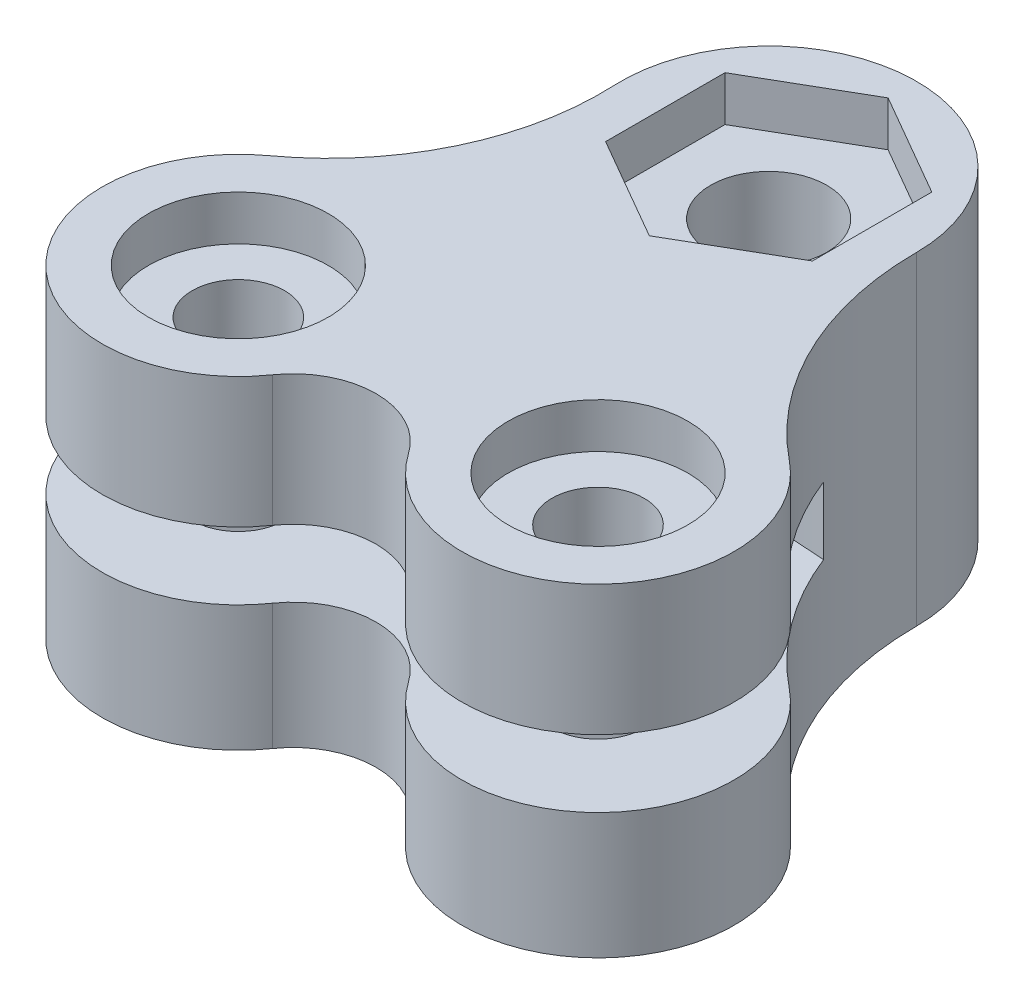
SolidWorks part; units mm, degrees
ref_plane "Front Plane" through (0, 0, 0) normal (0, 0, 1) x (1, 0, 0)
ref_plane "Top Plane" through (0, 0, 0) normal (0, 1, 0) x (1, 0, 0)
ref_plane "Right Plane" through (0, 0, 0) normal (1, 0, 0) x (0, 0, -1)
sketch "Sketch1" plane through (0, 0, 0) normal (0, 1, 0) x (1, 0, 0)
  line L0 (0, 0) -> (0, 133.35) construction
  line L1 (0, 157.5) -> (-10.448, 157.1531) construction
  line L2 (-12.7, 132.7439) -> (-12.7, 142.3578) construction
  line L3 (12.7, 132.7439) -> (12.7, 142.3578) construction
  line L4 (-12.7, 132.7439) -> (-3.0861, 132.7439) construction
  line L5 (12.7, 132.7439) -> (3.0861, 132.7439) construction
  line L6 (0, 157.5) -> (10.4521, 157.5) construction
  line L7 (-12.7, 132.7439) -> (-12.7, 123.13) construction
  line L8 (12.7, 132.7439) -> (12.7, 123.13) construction
  line L9 (-12.7, 132.7439) -> (-18.3509, 140.5217) construction
  line L10 (12.7, 132.7439) -> (18.3509, 140.5217) construction
  circle A0 centre (0, 0) radius 133.35 construction
  circle A1 centre (-12.7, 132.7439) radius 3.2639
  circle A2 centre (12.7, 132.7439) radius 3.2639
  arc A3 (-18.3509, 140.5217) -> (-4.8072, 127.2547) centre (-12.7, 132.7439) ccw
  arc A4 (18.3509, 140.5217) -> (4.8072, 127.2547) centre (12.7, 132.7439) cw
  circle A5 centre (0, 0) radius 157.5 construction
  circle A6 centre (0, 157.5) radius 4.1021
  arc A7 (10.4463, 157.1532) -> (-10.4403, 157.0036) centre (0, 157.5) ccw
  arc A8 (-10.448, 157.1531) -> (-18.3509, 140.5217) centre (-29.6618, 156.0897) cw
  arc A9 (10.4521, 157.5) -> (18.7238, 140.2366) centre (32.6027, 157.5) ccw
  arc A10 (4.8072, 127.2547) -> (-4.8072, 127.2547) centre (0, 123.9116) ccw
  dimension "D1" = 266.7
  dimension "D2" = 6.5278
  dimension "D5" = 315
  dimension "D6" = 8.2042
  dimension "D3" = 12.7
  dimension "D4" = 6.35
  dimension "D7" = 6.35
  dimension "D8" = 36
  dimension "D9" = 36
extrude "Boss-Extrude1" add sketch "Sketch1" along normal blind 22.86
ref_plane "Plane1" through (0, 8.89, 0) normal (0, -1, 0) x (-1, 0, 0)
sketch "Sketch2" plane through (0, 8.89, 0) normal (0, -1, 0) x (-1, 0, 0)
  circle A0 centre (0, 0) radius 149.225 construction
  arc A1 (-18.7238, 140.2366) -> (-4.8072, 127.2547) centre (-12.7, 132.7439) ccw construction
  arc A2 (4.8072, 127.2547) -> (-4.8072, 127.2547) centre (0, 123.9116) ccw construction
  arc A3 (4.8072, 127.2547) -> (18.3509, 140.5217) centre (12.7, 132.7439) ccw construction
  arc A4 (10.4403, 157.0036) -> (18.3509, 140.5217) centre (29.6618, 156.0897) ccw construction
  arc A5 (-18.7238, 140.2366) -> (-10.4521, 157.5) centre (-32.6027, 157.5) ccw construction
  arc A6 (-18.7238, 140.2366) -> (-4.8072, 127.2547) centre (-12.7, 132.7439) ccw
  arc A7 (4.8072, 127.2547) -> (-4.8072, 127.2547) centre (0, 123.9116) ccw
  arc A8 (4.8072, 127.2547) -> (18.3509, 140.5217) centre (12.7, 132.7439) ccw
  arc A9 (11.6154, 149.4092) -> (18.3509, 140.5217) centre (29.6618, 156.0897) ccw
  arc A10 (-18.7238, 140.2366) -> (-11.9944, 149.3792) centre (-32.6027, 157.5) ccw
  arc A11 (11.6154, 149.4092) -> (-11.9944, 149.3792) centre (0, 0) ccw
  circle A13 centre (0, 0) radius 149.86 construction
  point P18 (151.13, 0)
  dimension "D1" = 298.45
  dimension "D2" = 0.635
extrude "Cut-Extrude1" cut sketch "Sketch2" against normal blind 4.7625
sketch "Sketch3" plane through (0, 0, 0) normal (0, -1, 0) x (1, 0, 0)
  line L0 (-12.7, -132.7439) -> (-12.7, -125.9614) construction
  line L1 (-18.5737, -129.3526) -> (-18.5738, -136.1351)
  line L2 (-18.5738, -136.1351) -> (-12.7, -139.5263)
  line L3 (-12.7, -139.5263) -> (-6.8263, -136.1351)
  line L4 (-6.8263, -136.1351) -> (-6.8263, -129.3526)
  line L5 (-6.8263, -129.3526) -> (-12.7, -125.9614)
  line L6 (-12.7, -125.9614) -> (-18.5737, -129.3526)
  line L7 (0, -157.5) -> (0, -122.0589) construction
  line L8 (12.7, -132.7439) -> (12.7, -125.9614) construction
  line L9 (12.7, -125.9614) -> (18.5738, -129.3526)
  line L10 (6.8263, -129.3526) -> (12.7, -125.9614)
  line L11 (6.8263, -136.1351) -> (6.8263, -129.3526)
  line L12 (12.7, -139.5263) -> (6.8263, -136.1351)
  line L13 (18.5738, -136.1351) -> (12.7, -139.5263)
  line L14 (18.5738, -129.3526) -> (18.5738, -136.1351)
  circle A0 centre (0, -157.5) radius 8.1915
  circle A1 centre (-12.7, -132.7439) radius 5.8737 construction
  circle A2 centre (12.7, -132.7439) radius 5.8737 construction
  dimension "D1" = 16.383
  dimension "D2" = 11.7475
extrude "bottom-cuts" cut sketch "Sketch3" against normal blind 6.096
sketch "Sketch4" plane through (0, 22.86, 0) normal (0, 1, 0) x (1, 0, 0)
  line L0 (0, 129.767) -> (0, 157.5) construction
  line L1 (0, 157.5) -> (0, 165.9322) construction
  line L2 (7.3025, 161.7161) -> (0, 165.9322)
  line L3 (0, 165.9322) -> (-7.3025, 161.7161)
  line L4 (-7.3025, 161.7161) -> (-7.3025, 153.2839)
  line L5 (-7.3025, 153.2839) -> (0, 149.0678)
  line L6 (0, 149.0678) -> (7.3025, 153.2839)
  line L7 (7.3025, 153.2839) -> (7.3025, 161.7161)
  circle A0 centre (-12.7, 132.7439) radius 6.35
  arc A1 (4.8072, 127.2547) -> (-4.8072, 127.2547) centre (0, 123.9116) ccw construction
  circle A2 centre (12.7, 132.7439) radius 6.35
  circle A3 centre (0, 157.5) radius 7.3025 construction
  dimension "D1" = 12.7
  dimension "D2" = 14.605
extrude "top-cuts" cut sketch "Sketch4" against normal blind 3.175
equation "\"D7@Sketch1\"=\"D4@Sketch1\""
